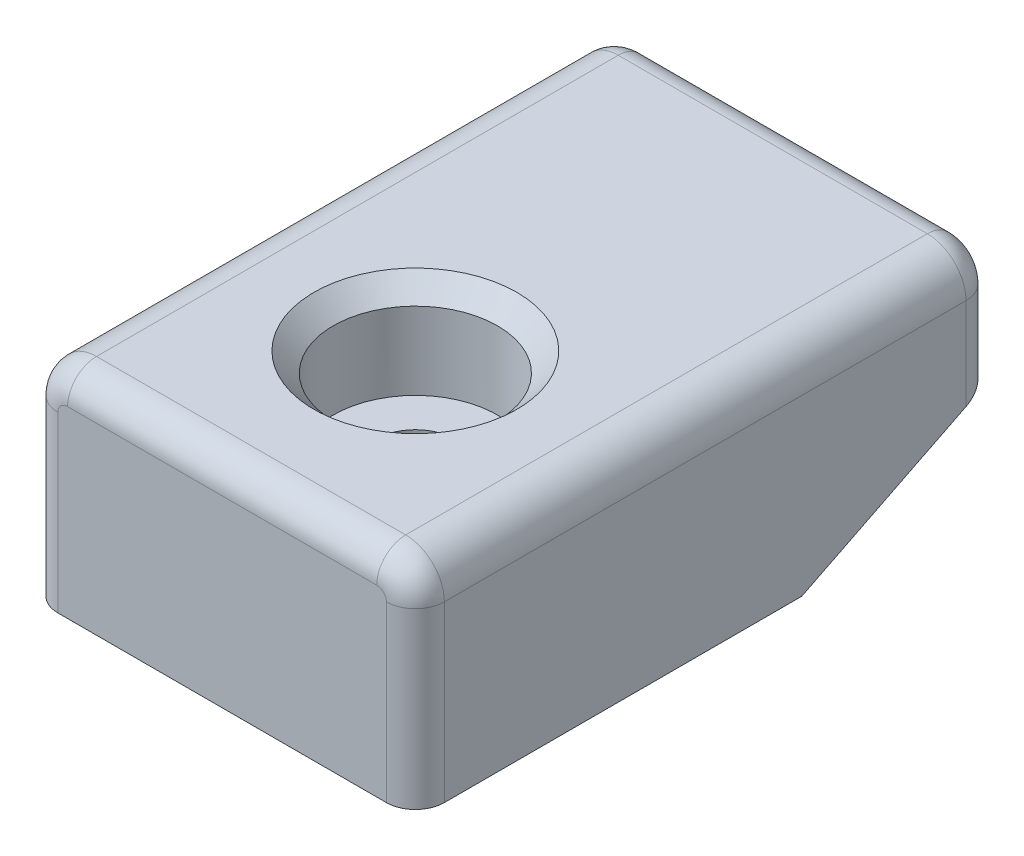
SolidWorks part; units mm, degrees
material "PET"
ref_plane "Front Plane" through (0, 0, 0) normal (0, 0, 1) x (1, 0, 0)
ref_plane "Top Plane" through (0, 0, 0) normal (0, 1, 0) x (1, 0, 0)
ref_plane "Right Plane" through (0, 0, 0) normal (1, 0, 0) x (0, 0, -1)
sketch "Sketch1" plane through (0, 0, 0) normal (0, 1, 0) x (1, 0, 0)
  line L0 (-16.6746, -29.9109) -> (-5.63, -29.9109) construction
  line L1 (-20, -29.9109) -> (20, -29.9109)
  line L2 (-20, -29.9109) -> (-20, 30.0891)
  line L3 (-20, 30.0891) -> (20, 30.0891)
  line L4 (20, -29.9109) -> (20, 30.0891)
  line L5 (-20, -29.9109) -> (20, 30.0891) construction
  line L6 (-20, 30.0891) -> (20, -29.9109) construction
  line L7 (20, -26.7409) -> (20, -15.5409) construction
  circle A1 centre (0, -9.9109) radius 4.15
  point P0 (0, 0.0891)
  dimension "D3" = 8.3
  dimension "D1" = 60
  dimension "D2" = 40
extrude "Boss-Extrude1" add sketch "Sketch1" along normal mid plane 22
sketch "Sketch2" plane through (0, 11, 0) normal (0, 1, 0) x (1, 0, 0)
  circle A0 centre (0, -9.9109) radius 8.5
  dimension "D1" = 17
extrude "Cut-Extrude1" cut sketch "Sketch2" against normal blind 10
fillet "Fillet1" radius 4 2 edges at (-20, 11, -0.0891) (20, 11, -0.0891)
chamfer "Chamfer1" distance 2 angle 45 1 edges at (0, 11, 18.4109)
chamfer "Chamfer2" distance 20 distance2 10 1 edges at (0, -11, -30.0891)
fillet "Fillet2" radius 3 10 edges at (20, 3, -30.0891) (18.8284, 9.8284, -30.0891) (-20, 3, -30.0891) (-18.8284, 9.8284, -30.0891) (20, -2, 29.9109) (18.8284, 9.8284, 29.9109) (0, 11, 29.9109) (-18.8284, 9.8284, 29.9109) (0, 11, -30.0891) (-20, -2, 29.9109)
